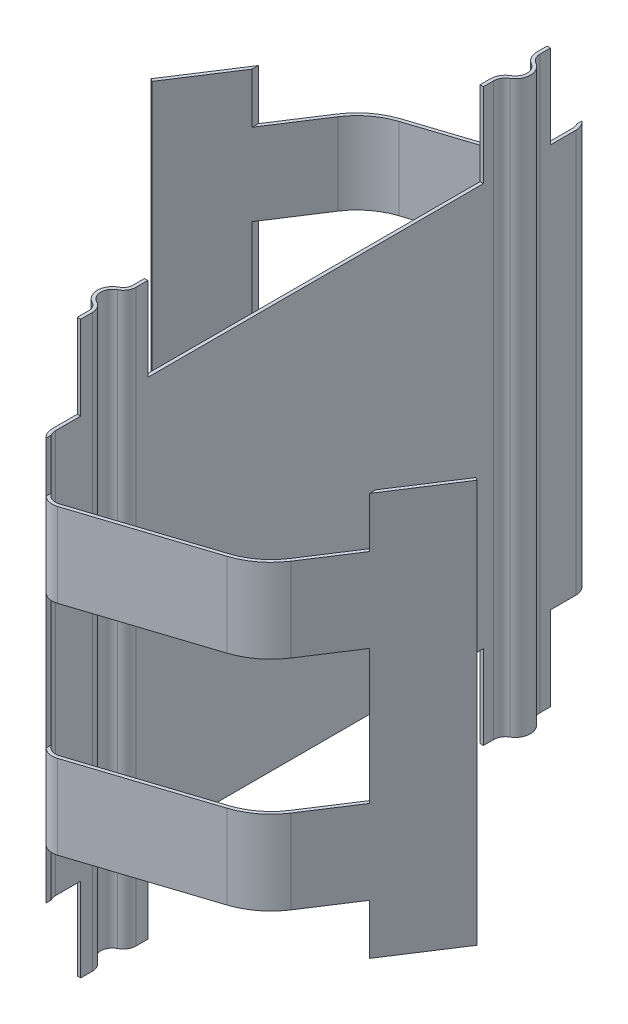
SolidWorks part; units mm, degrees
material "AISI 316 Stainless Steel Sheet (SS)"
ref_plane "Front Plane" through (0, 0, 0) normal (0, 0, 1) x (1, 0, 0)
ref_plane "Top Plane" through (0, 0, 0) normal (0, 1, 0) x (1, 0, 0)
ref_plane "Right Plane" through (0, 0, 0) normal (1, 0, 0) x (0, 0, -1)
ref_plane "Plane1" through (0, 0, 0) normal (0, 1, 0) x (1, 0, 0)
sketch "Sketch1" plane through (0, 0, 0) normal (0, 1, 0) x (1, 0, 0)
  line L0 (-0.5236, 8.1317) -> (-4.3278, 6.8956)
  line L1 (-5.3871, 6.0828) -> (-7.5657, 2.7281)
  line L2 (0.5236, -8.1282) -> (4.3278, -6.8921)
  line L3 (5.3871, -6.0793) -> (7.5657, -2.7246)
  line L4 (0, 7.7513) -> (0, 6.6928)
  line L5 (0, -6.6523) -> (0, -7.7478)
  line L6 (0, 5.3072) -> (0, -5.35)
  arc A0 (0, 7.7513) -> (-0.5236, 8.1317) centre (-0.4, 7.7513) ccw
  arc A1 (-4.3278, 6.8956) -> (-5.3871, 6.0828) centre (-3.7098, 4.9935) ccw
  arc A2 (0, -7.7478) -> (0.5236, -8.1282) centre (0.4, -7.7478) ccw
  arc A3 (4.3278, -6.8921) -> (5.3871, -6.0793) centre (3.7098, -4.99) ccw
  arc A4 (0, 6.6928) -> (0.2, 6.3464) centre (0.4, 6.6928) ccw
  arc A5 (0.2, 5.6536) -> (0.2, 6.3464) centre (0, 6) ccw
  arc A6 (0.2, 5.6536) -> (0, 5.3072) centre (0.4, 5.3072) ccw
  arc A7 (0, -6.6523) -> (-0.1808, -6.3579) centre (-0.33, -6.6523) ccw
  arc A8 (-0.1808, -5.6444) -> (-0.1808, -6.3579) centre (0, -6.0012) ccw
  arc A9 (-0.1808, -5.6444) -> (0, -5.35) centre (-0.33, -5.35) ccw
extrude "Extrude-Thin1" add sketch "Sketch1" along normal blind 8.5 and the other way blind 8.5 thin thin type mid plane wall 0.1
ref_plane "Plane2" through (0, 0, 0) normal (1, 0, 0) x (0, 0, -1)
sketch "Sketch2" plane through (0, 0, 0) normal (1, 0, 0) x (0, 0, -1)
  line L0 (5, 8.5) -> (-5, 8.5)
  line L1 (-5, 8.5) -> (-5, 6)
  line L2 (-5, 6) -> (5, 6)
  line L3 (5, 6) -> (5, 8.5)
  line L4 (5, -8.5) -> (-5, -8.5)
  line L5 (-5, -8.5) -> (-5, -6)
  line L6 (-5, -6) -> (5, -6)
  line L7 (5, -6) -> (5, -8.5)
  line L8 (7, 8.5) -> (9.5, 8.5)
  line L9 (9.5, 8.5) -> (9.5, 6)
  line L10 (9.5, 6) -> (7, 6)
  line L11 (7, 6) -> (7, 8.5)
  line L12 (-7, 8.5) -> (-9.5, 8.5)
  line L13 (-9.5, 8.5) -> (-9.5, 6)
  line L14 (-9.5, 6) -> (-7, 6)
  line L15 (-7, 6) -> (-7, 8.5)
  line L16 (7, -8.5) -> (9.5, -8.5)
  line L17 (9.5, -8.5) -> (9.5, -6)
  line L18 (9.5, -6) -> (7, -6)
  line L19 (7, -6) -> (7, -8.5)
  line L20 (-7, -8.5) -> (-9.5, -8.5)
  line L21 (-9.5, -8.5) -> (-9.5, -6)
  line L22 (-9.5, -6) -> (-7, -6)
  line L23 (-7, -6) -> (-7, -8.5)
  dimension "D1" = 2
  dimension "D2" = 2
  dimension "D3" = 2
  dimension "D4" = 2
extrude "Extrude1" cut sketch "Sketch2" along normal blind 10 and the other way blind 10
ref_plane "Plane3" through (0, 0, 0) normal (0, 0, 1) x (-1, 0, 0)
sketch "Sketch3" plane through (0, 0, 0) normal (0, 0, 1) x (-1, 0, 0)
  line L0 (-0.1, -8.5) -> (-6.35, -8.5)
  line L1 (-6.35, -8.5) -> (-6.35, -4.5)
  line L2 (-6.35, -4.5) -> (-0.1, -4.5)
  line L3 (-0.1, -4.5) -> (-0.1, -8.5)
  line L4 (-0.1, -2) -> (-6.35, -2)
  line L5 (-6.35, -2) -> (-6.35, 2)
  line L6 (-6.35, 2) -> (-0.1, 2)
  line L7 (-0.1, 2) -> (-0.1, -2)
  line L8 (-0.1, 8.5) -> (-6.35, 8.5)
  line L9 (-6.35, 8.5) -> (-6.35, 4.5)
  line L10 (-6.35, 4.5) -> (-0.1, 4.5)
  line L11 (-0.1, 4.5) -> (-0.1, 8.5)
  dimension "D1" = 6.25
extrude "Extrude2" cut sketch "Sketch3" along normal blind 10
ref_plane "Plane4" through (0, 0, 0) normal (0, 0, 1) x (-1, 0, 0)
sketch "Sketch4" plane through (0, 0, 0) normal (0, 0, 1) x (-1, 0, 0)
  line L0 (0.1, 8.5) -> (6.35, 8.5)
  line L1 (6.35, 8.5) -> (6.35, 4.5)
  line L2 (6.35, 4.5) -> (0.1, 4.5)
  line L3 (0.1, 4.5) -> (0.1, 8.5)
  line L4 (0.1, 1.9372) -> (6.35, 1.9372)
  line L5 (6.35, 1.9372) -> (6.35, -2.0628)
  line L6 (6.35, -2.0628) -> (0.1, -2.0628)
  line L7 (0.1, -2.0628) -> (0.1, 1.9372)
  line L8 (0.1, -4.5) -> (6.35, -4.5)
  line L9 (6.35, -4.5) -> (6.35, -8.5)
  line L10 (6.35, -8.5) -> (0.1, -8.5)
  line L11 (0.1, -8.5) -> (0.1, -4.5)
extrude "Extrude3" cut sketch "Sketch4" against normal blind 10
